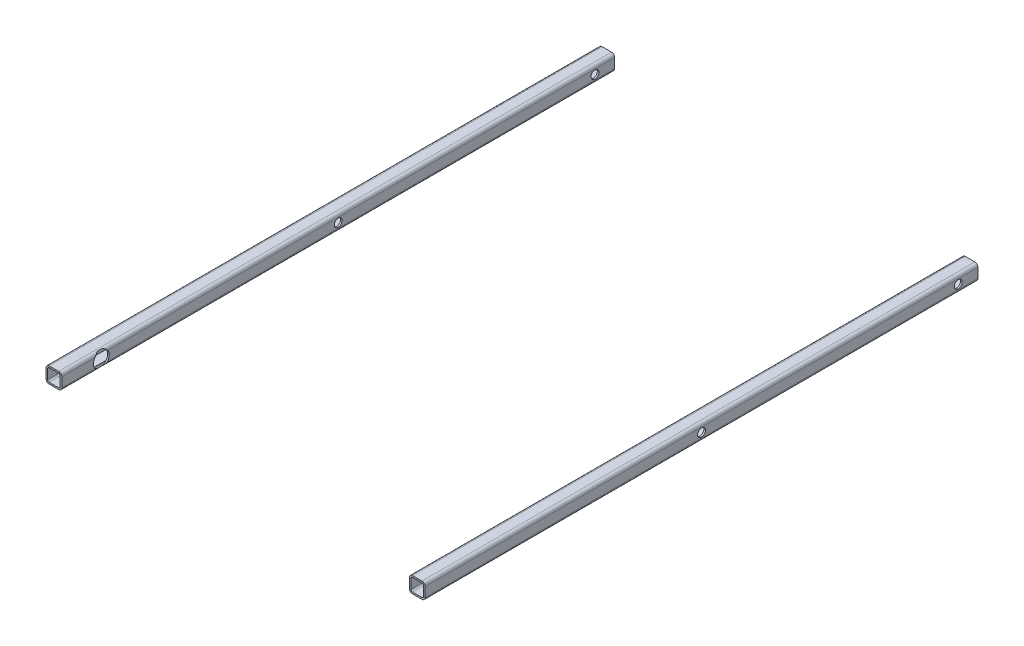
SolidWorks part; units mm, degrees
ref_plane "Front Plane" through (0, 0, 0) normal (0, 0, 1) x (1, 0, 0)
ref_plane "Top Plane" through (0, 0, 0) normal (0, 1, 0) x (1, 0, 0)
ref_plane "Right Plane" through (0, 0, 0) normal (1, 0, 0) x (0, 0, -1)
sketch "Sketch1" plane through (0, 0, 0) normal (0, 1, 0) x (1, 0, 0)
  line L2 (190, 450) -> (190, -250)
  line L4 (-270, 450) -> (-270, -250)
  point P0 (0, 0)
  dimension "D1" = 460
  dimension "D2" = 700
other "Square tube - configured 20 X 20 X 2(1)"
ref_plane "Plane1" through (-270, 0, -450) normal (0, 0, 1) x (1, 0, 0)
sketch "Sketch17" plane through (-270, 0, -450) normal (0, 0, 1) x (1, 0, 0)
  line L0 (-6, -8) -> (6, -8)
  line L1 (-8, -6) -> (-8, 6)
  line L2 (6, 8) -> (-6, 8)
  line L3 (8, 6) -> (8, -6)
  line L4 (-6, -10) -> (6, -10)
  line L5 (-10, -6) -> (-10, 6)
  line L6 (6, 10) -> (-6, 10)
  line L7 (10, 6) -> (10, -6)
  arc A0 (10, 6) -> (6, 10) centre (6, 6) ccw
  arc A1 (6, -10) -> (10, -6) centre (6, -6) ccw
  arc A2 (-10, -6) -> (-6, -10) centre (-6, -6) ccw
  arc A3 (-6, 10) -> (-10, 6) centre (-6, 6) ccw
  arc A4 (-6, 8) -> (-8, 6) centre (-6, 6) ccw
  arc A5 (8, 6) -> (6, 8) centre (6, 6) ccw
  arc A6 (6, -8) -> (8, -6) centre (6, -6) ccw
  arc A7 (-8, -6) -> (-6, -8) centre (-6, -6) ccw
  point P0 (-10, 0)
  point P1 (10, 0)
  point P2 (0, 10)
  point P3 (0, -10)
  point P4 (0, 0)
  point P5 (-10, -10)
  point P6 (10, -10)
  point P7 (10, 10)
  point P8 (-10, 10)
  point P33 (0, 0)
  dimension "D1" = 4
  dimension "Thickness" = 2
  dimension "V_leg" = 20
sketch "Sketch15" plane through (0, 0, 0) normal (1, 0, 0) x (0, 0, -1)
  line L0 (-250, 0) -> (450, 0) construction
  line L1 (-250, -6) -> (-250, 6) construction
  line L2 (450, -6) -> (450, 6) construction
  circle A0 centre (100, 0) radius 5
  dimension "D1" = 10
extrude "Cut-Extrude1" cut sketch "Sketch15" against normal through all both and the other way through all
sketch "Sketch18" plane through (180, 0, 0) normal (-1, 0, 0) x (0, 0, 1)
  line L0 (-450, 6) -> (-450, -6) construction
  circle A0 centre (-425, 0) radius 5
  dimension "D1" = 10
  dimension "D2" = 25
extrude "Cut-Extrude2" cut sketch "Sketch18" against normal through all both and the other way through all
sketch "Sketch13" plane through (180, 0, 0) normal (-1, 0, 0) x (0, 0, 1)
  line L7 (250, 6) -> (250, -6) construction
  circle A0 centre (200, 0) radius 10
  dimension "D1" = 50
extrude "Cut-Extrude3" cut sketch "Sketch13" against normal blind 2 and the other way blind 442
